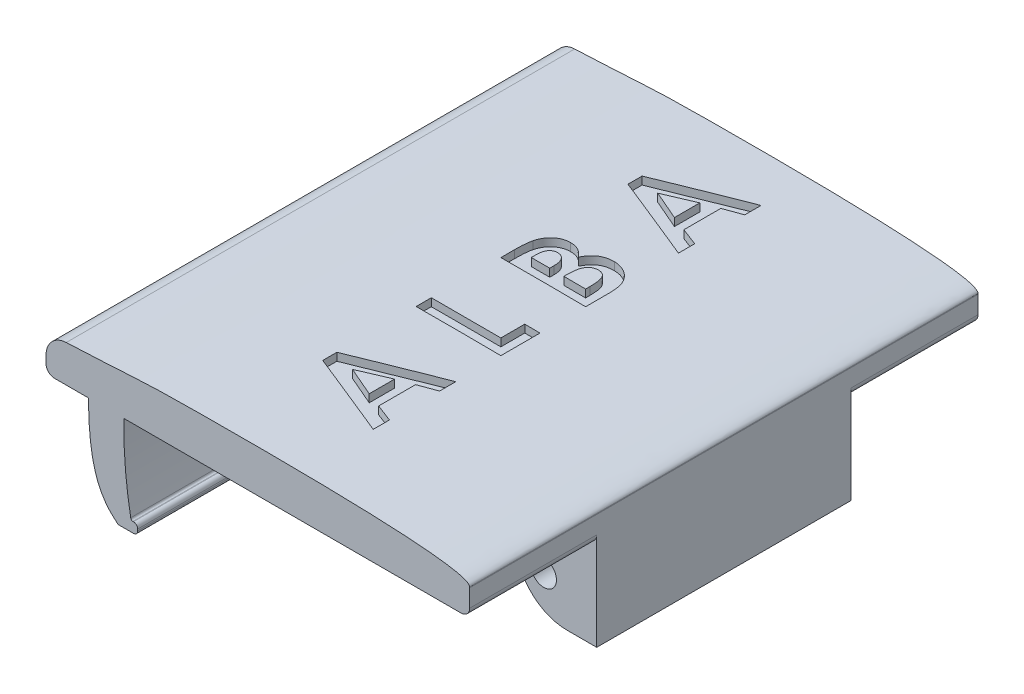
SolidWorks part; units mm, degrees
ref_plane "Front Plane" through (0, 0, 0) normal (0, 0, 1) x (1, 0, 0)
ref_plane "Top Plane" through (0, 0, 0) normal (0, 1, 0) x (1, 0, 0)
ref_plane "Right Plane" through (0, 0, 0) normal (1, 0, 0) x (0, 0, -1)
sketch "Sketch1" plane through (0, 0, 0) normal (0, 0, 1) x (1, 0, 0)
  line L0 (3.0958, 5.3845) -> (3.8958, 5.3845)
  line L1 (4.5954, 3.1466) -> (4.9599, 3.1466)
  line L2 (12.8958, 5.5845) -> (12.8958, 6.0019)
  line L3 (5.0599, 3.2466) -> (5.0599, 3.2845)
  line L4 (4.9599, 3.3845) -> (4.9458, 3.3845)
  line L5 (4.7328, 5.3845) -> (4.8958, 5.3845)
  line L6 (4.8958, 5.3845) -> (12.6958, 5.3845)
  line L8 (2.8958, 5.5845) -> (2.8958, 5.7564)
  arc A0 (4.9599, 3.1466) -> (5.0599, 3.2466) centre (4.9599, 3.2466) ccw
  arc A1 (5.0599, 3.2845) -> (4.9599, 3.3845) centre (4.9599, 3.2845) ccw
  arc A2 (4.9458, 3.3845) -> (4.8958, 3.4345) centre (4.9458, 3.4345) cw
  arc A4 (2.8958, 5.7564) -> (3.3743, 6.2559) centre (3.3958, 5.7564) cw
  arc A5 (12.8958, 6.0019) -> (12.8954, 6.02) centre (12.3958, 6.0019) ccw
  arc A6 (12.6958, 5.3845) -> (12.8958, 5.5845) centre (12.6958, 5.5845) ccw
  arc A7 (3.0958, 5.3845) -> (2.8958, 5.5845) centre (3.0958, 5.5845) cw
  spline S0 degree 2 poles (4.8958, 3.4345) (4.7182, 4.3967) (4.7328, 5.3845) knots 0 0 0 1 1 1
  spline S1 degree 3 poles (3.8958, 5.3845) (3.9037, 4.8762) (3.9408, 4.342) (4.2336, 3.3666) (4.592, 3.1741) (4.5954, 3.1466) knots 0 0 0 0 0.345637 0.444283 0.986455 0.986455 0.986455 0.986455
  spline S2 degree 3 poles (12.8954, 6.02) (12.8824, 6.3778) (4.4521, 6.4084) (5.3192, 6.3397) (3.3743, 6.2559) knots 0.048294 0.048294 0.048294 0.048294 0.480382 0.960763 0.960763 0.960763 0.960763
  point P16 (4.8958, 3.3845)
  point P29 (2.8958, 5.3845)
  dimension "D3" = 0.1
  dimension "D5" = 0.05
  dimension "D8" = 0.5
  dimension "D9" = 0.2
  dimension "D1" = 1
  dimension "D4" = 2
  dimension "D7" = 10
extrude "Boss-Extrude1" add sketch "Sketch1" along normal blind 12
sketch "Sketch2" plane through (0, 5.3845, 0) normal (0, -1, 0) x (1, 0, 0)
  line L0 (12.8958, 12) -> (12.8958, 0) construction
  line L1 (10.9958, 9) -> (12.8958, 9)
  line L2 (10.9958, 9) -> (10.9958, 3)
  line L3 (10.9958, 3) -> (12.8958, 3)
  line L4 (12.8958, 9) -> (12.8958, 3)
  line L5 (4.7328, 12) -> (12.6958, 12) construction
  dimension "D1" = 1.9
  dimension "D2" = 6
  dimension "D3" = 3
extrude "Boss-Extrude2" add sketch "Sketch2" along normal blind 2.1 and the other way blind 0.3
fillet "Fillet1" radius 1.2 1 edges at (10.9958, 3.2845, 6)
sketch "Sketch3" plane through (0, 0, 9) normal (0, 0, 1) x (1, 0, 0)
  line L0 (12.8958, 3.2845) -> (12.1958, 3.2845) construction
  line L1 (12.8958, 5.5845) -> (12.8958, 3.2845) construction
  circle A0 centre (11.6458, 4.1845) radius 0.3
  dimension "D1" = 0.9
  dimension "D2" = 1.25
extrude "Cut-Extrude1" cut sketch "Sketch3" against normal through all
ref_plane "Plane1" through (0, 6.5, 0) normal (0, 1, 0) x (-1, 0, 0)
sketch "Sketch8" plane through (0, 6.5, 0) normal (0, 1, 0) x (-1, 0, 0)
  line L0 (-8.8958, 10.3144) -> (-8.8958, 1.0507)
  line L1 (-12.8958, 12) -> (-12.8958, 0) construction
  dimension "D1" = 4
sketch "Sketch9" plane through (0, 6.5, 0) normal (0, 1, 0) x (-1, 0, 0)
  text T0 "<b>A L B A</b>" font "Century Gothic" height 2
extrude "Cut-Extrude3" cut sketch "Sketch9" against normal blind 0.3
